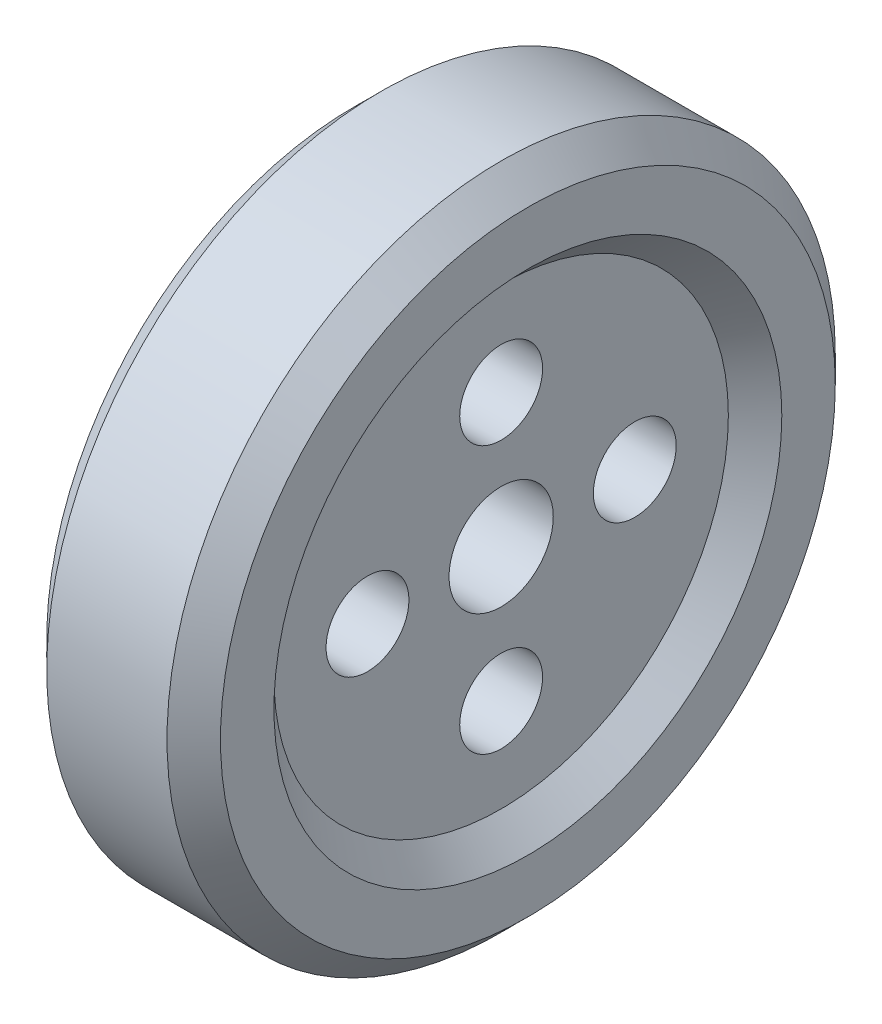
SolidWorks part; units mm, degrees
ref_plane "Ön Düzlem" through (0, 0, 0) normal (0, 0, 1) x (1, 0, 0)
ref_plane "Üst Düzlem" through (0, 0, 0) normal (0, 1, 0) x (1, 0, 0)
ref_plane "Sağ Düzlem" through (0, 0, 0) normal (1, 0, 0) x (0, 0, -1)
sketch "Çizim2" plane through (0, 0, 0) normal (0, 0, 1) x (1, 0, 0)
  line L0 (-818.471, 390.989) -> (-798.471, 370.989)
  line L1 (-690.9734, 140.989) -> (-1013.0935, 140.989) construction
  line L2 (-908.471, 310.989) -> (-908.471, 140.989)
  line L3 (-908.471, 140.989) -> (-818.471, 140.989)
  line L4 (-818.471, 310.989) -> (-818.471, 140.989)
  line L6 (-908.471, 390.989) -> (-818.471, 390.989)
  line L7 (-928.471, 370.989) -> (-928.471, 330.989)
  line L9 (-798.471, 370.989) -> (-798.471, 330.989)
  line L13 (-928.471, 370.989) -> (-908.471, 390.989)
  line L18 (-928.471, 330.989) -> (-908.471, 310.989)
  line L19 (-818.471, 310.989) -> (-798.471, 330.989)
  point P5 (-928.471, 390.989)
  point P6 (-798.471, 310.989)
  point P7 (-928.471, 310.989)
  point P8 (-798.471, 390.989)
  point P10 (-928.471, -29.011)
  point P11 (-798.471, -109.011)
  point P12 (-928.471, -109.011)
  point P13 (-798.471, -29.011)
  dimension "D3" = 130
  dimension "D4" = 130
  dimension "D5" = 80
  dimension "D6" = 80
revolve "Döndür1" add sketch "Çizim2" angle 360 about L1
sketch "Çizim3" plane through (-908.471, 0, 0) normal (-1, 0, 0) x (0, 0, 1)
  circle A0 centre (0, 140.989) radius 39
  circle A1 centre (0, 140.989) radius 100 construction
  circle A2 centre (-100, 140.989) radius 31
  circle A3 centre (0, 240.989) radius 31
  circle A4 centre (100, 140.989) radius 31
  circle A5 centre (0, 40.989) radius 31
  point P15 (0, 140.989)
  dimension "D1" = 78
  dimension "D2" = 200
  dimension "D3" = 62
  dimension "D4" = 4
extrude "Kes-Ekstrüzyon1" cut sketch "Çizim3" against normal through all
